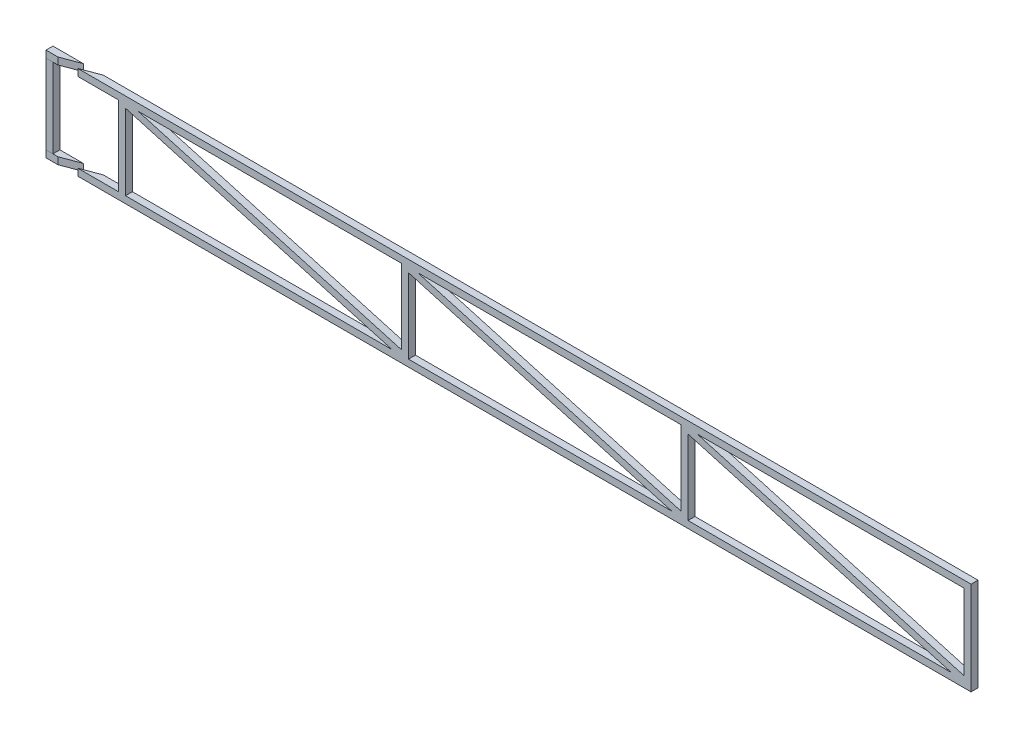
SolidWorks part; units mm, degrees
material "Balsa"
ref_plane "Front Plane" through (0, 0, 0) normal (0, 0, 1) x (1, 0, 0)
ref_plane "Top Plane" through (0, 0, 0) normal (0, 1, 0) x (1, 0, 0)
ref_plane "Right Plane" through (0, 0, 0) normal (1, 0, 0) x (0, 0, -1)
sketch "Sketch1" plane through (0, 0, 0) normal (0, 0, 1) x (1, 0, 0)
  line L0 (-18.175, 48.175) -> (18.175, 48.175)
  line L4 (405, 11.825) -> (405, 15)
  line L5 (-15, 45) -> (15, 45)
  line L7 (-15, 15) -> (15, 15)
  line L10 (405, 11.825) -> (405, 15)
  line L14 (-18.175, 11.825) -> (18.175, 11.825)
  line L16 (18.175, 48.175) -> (405, 48.175)
  line L17 (18.175, 11.825) -> (405, 11.825)
  line L18 (15, 45) -> (405, 45)
  line L19 (15, 15) -> (405, 15)
  line L20 (-18.175, 48.175) -> (-18.175, 45)
  line L21 (-18.175, 48.175) -> (-18.175, 11.825) construction
  line L22 (-15, 45) -> (-15, 15) construction
  line L23 (15, 45) -> (15, 15) construction
  line L24 (-18.175, 45) -> (-15, 45)
  line L25 (18.175, 48.175) -> (18.175, 11.825) construction
  line L26 (405, 45) -> (405, 48.175)
  line L27 (405, 45) -> (405, 48.175)
  line L28 (-18.175, 11.825) -> (-18.175, 15)
  line L29 (-18.175, 15) -> (-15, 15)
  point P4 (0, 30)
  dimension "D3" = 30
  dimension "D5" = 3.175
extrude "Boss-Extrude1" add sketch "Sketch1" along normal blind 3.175 contours L18 L26 L16 L0 L20 L24 L5 | L29 L28 L14 L17 L4 L19 L7
sketch "Sketch2" plane through (0, 0, 3.175) normal (0, 0, 1) x (1, 0, 0)
  line L0 (-18.175, 48.175) -> (405, 48.175) construction
  line L1 (-18.175, 11.825) -> (-15, 11.825)
  line L2 (-18.175, 11.825) -> (-18.175, 48.175)
  line L3 (-18.175, 48.175) -> (-15, 48.175)
  line L4 (-15, 11.825) -> (-15, 48.175)
  line L5 (-18.175, 11.825) -> (405, 11.825) construction
  line L6 (-15, 48.175) -> (15, 48.175)
  line L7 (-15, 48.175) -> (-15, 11.825)
  line L8 (-15, 11.825) -> (15, 11.825)
  line L9 (15, 48.175) -> (15, 11.825)
  line L10 (18.175, 30) -> (401.825, 30) construction
  line L11 (15, 48.175) -> (18.175, 48.175)
  line L12 (15, 48.175) -> (15, 11.825)
  line L13 (15, 11.825) -> (18.175, 11.825)
  line L14 (18.175, 48.175) -> (18.175, 11.825)
  line L15 (405, 48.175) -> (401.825, 48.175)
  line L16 (405, 48.175) -> (405, 11.825)
  line L17 (405, 11.825) -> (401.825, 11.825)
  line L18 (401.825, 48.175) -> (401.825, 11.825)
  line L19 (210, 30) -> (210, 38.7375) construction
  line L20 (18.175, 38.7375) -> (210, 38.7375) construction
  line L21 (114.0875, 38.7375) -> (114.0875, 45)
  line L22 (-18.175, 45) -> (405, 45) construction
  line L23 (210, 38.7375) -> (401.825, 38.7375) construction
  line L24 (305.9125, 38.7375) -> (305.9125, 45) construction
  line L25 (115.675, 11.825) -> (120.0251, 11.825)
  line L26 (115.675, 11.825) -> (112.5, 11.825)
  line L27 (115.675, 11.825) -> (115.675, 48.175)
  line L28 (114.1836, 48.175) -> (112.5, 48.175)
  line L29 (112.5, 11.825) -> (112.5, 48.175)
  line L30 (114.0875, 30) -> (113.3243, 38.7375) construction
  line L31 (115.675, 48.175) -> (112.5, 11.825) construction
  line L32 (211.5875, 11.825) -> (208.4125, 11.825)
  line L33 (211.5875, 11.825) -> (211.5875, 48.175)
  line L34 (211.5875, 48.175) -> (208.4125, 48.175)
  line L35 (208.4125, 11.825) -> (208.4125, 48.175)
  line L36 (211.5875, 11.825) -> (209.2368, 38.7375) construction
  line L37 (211.5875, 48.175) -> (208.4125, 11.825) construction
  line L38 (304.325, 11.825) -> (307.5, 11.825)
  line L39 (304.325, 11.825) -> (304.325, 48.175)
  line L40 (304.325, 48.175) -> (307.5, 48.175)
  line L41 (307.5, 11.825) -> (307.5, 48.175)
  line L42 (304.325, 11.825) -> (307.5, 48.175) construction
  line L43 (304.325, 48.175) -> (307.5, 11.825) construction
  line L44 (120.0251, 11.825) -> (208.4125, 46.4699)
  line L45 (111.3249, 11.825) -> (112.5417, 12.3019)
  line L46 (208.4125, 48.175) -> (204.0624, 48.175)
  line L47 (115.675, 13.5301) -> (204.0624, 48.175)
  point P36 (114.0875, 30)
  point P45 (305.9125, 30)
  line B0 (22.5897, 11.825) -> (112.5, 46.4737)
  line B1 (18.175, 13.5263) -> (108.0853, 48.175)
  line B2 (108.0853, 48.175) -> (112.5, 48.175)
  line B3 (18.175, 11.825) -> (22.5897, 11.825)
  line B4 (211.5875, 11.825) -> (215.9376, 11.825)
  line B5 (215.9376, 11.825) -> (304.325, 46.4699)
  line B6 (304.325, 48.175) -> (299.9749, 48.175)
  line B7 (211.5875, 13.5301) -> (299.9749, 48.175)
  line B8 (311.9147, 11.825) -> (401.825, 46.4737)
  line B9 (307.5, 13.5263) -> (397.4103, 48.175)
  line B10 (397.4103, 48.175) -> (401.825, 48.175)
  line B11 (307.5, 11.825) -> (311.9147, 11.825)
  dimension "D1" = 3.175
  dimension "D2" = 30
  dimension "D3" = 3.175
  dimension "D4" = 3.175
  dimension "D5" = 3.175
  dimension "D6" = 3.175
  dimension "D7" = 3.175
  dimension "D8" = 0
  dimension "D10" = 0
  dimension "D9" = 0
  dimension "D11" = 0
sketch_block_instance "Block1-1"
sketch_block "Block1"
sketch_block_instance "Block2-1"
sketch_block "Block2"
sketch_block_instance "Block1-3"
extrude "Boss-Extrude2" add sketch "Sketch2" along normal blind 3.175
sketch "Sketch3" plane through (405, 0, 0) normal (1, 0, 0) x (0, 0, -1)
  line L1 (-6.35, 11.825) -> (-3.175, 11.825)
  line L2 (-6.35, 11.825) -> (-6.35, 8.65)
  line L3 (-6.35, 8.65) -> (-3.175, 8.65)
  line L4 (-3.175, 11.825) -> (-3.175, 8.65)
  line L5 (-6.35, 48.175) -> (-3.175, 48.175)
  line L6 (-6.35, 48.175) -> (-6.35, 51.35)
  line L7 (-6.35, 51.35) -> (-3.175, 51.35)
  line L8 (-3.175, 48.175) -> (-3.175, 51.35)
  dimension "D1" = 3.175
  dimension "D2" = 3.175
extrude "Boss-Extrude8" add sketch "Sketch3" against normal up to surface (423.175 mm away) separate body contours L8 L7 L6 M2 | L4 L2 L3 M4 up to face at (-18.175, 30, 2.3812)
sketch "Sketch4" plane through (405, 0, 0) normal (1, 0, 0) x (0, 0, -1)
  line L1 (-3.175, 48.175) -> (0, 48.175)
  line L2 (-3.175, 48.175) -> (-3.175, 11.825)
  line L3 (-3.175, 11.825) -> (0, 11.825)
  line L4 (0, 48.175) -> (0, 11.825)
extrude "Cut-Extrude1" cut sketch "Sketch4" against normal through all
sketch "Sketch5" plane through (0, 8.65, 0) normal (0, -1, 0) x (1, 0, 0)
  line L17 (193.4125, 3.175) -> (193.4125, -106.4437) construction
  line L22 (-26.8415, 33.7017) -> (-103.7417, -72.6912)
  line L24 (377.5812, -136.0518) -> (376.4702, -139.0261)
  line L25 (-18.175, 6.35) -> (406.5875, 6.35)
  line L26 (405, 3.175) -> (-18.175, 3.175)
  line L27 (405, 6.35) -> (-18.175, 6.35)
  line L28 (377.5812, -136.0518) -> (4.8614, 3.175)
  line L29 (-12.7117, 6.35) -> (-26.8415, 33.7017)
  line L30 (403.4125, 6.35) -> (403.4125, -137.0625)
  line L31 (376.4702, -139.0261) -> (-4.212, 3.175)
  line L32 (-12.7117, 6.35) -> (-3.6383, 6.35)
  line L33 (406.5875, 6.35) -> (406.5875, -140.2375)
  line L34 (4.8614, 3.175) -> (-3.6383, 6.35)
  line L35 (-4.212, 3.175) -> (-12.7117, 6.35)
  line L36 (405, 6.35) -> (405, -138.65)
  arc A1 (372.1591, -137.4157) -> (373.2701, -134.4414) centre (380, -138.65) cw
extrude "Cut-Extrude7" cut sketch "Sketch5" against normal blind 3.175 contours L35 L26 L34 M6
sketch "Sketch9" plane through (0, 51.35, 0) normal (0, 1, 0) x (1, 0, 0)
  line L0 (391.037, -3.175) -> (399.5367, -6.35) construction
  line L1 (391.037, -3.175) -> (399.5367, -6.35)
  line L2 (381.9636, -3.175) -> (390.4633, -6.35) construction
  line L3 (391.037, -3.175) -> (399.5367, -6.35)
  line L4 (381.9636, -3.175) -> (390.4633, -6.35)
  line L5 (381.9636, -3.175) -> (391.037, -3.175)
  line L6 (399.5367, -6.35) -> (390.4633, -6.35)
  line L7 (-4.212, -3.175) -> (-12.7117, -6.35) construction
  line L8 (4.8614, -3.175) -> (-3.6383, -6.35) construction
  line L9 (-4.212, -3.175) -> (-12.7117, -6.35)
  line L10 (4.8614, -3.175) -> (-3.6383, -6.35)
  line L11 (-12.7117, -6.35) -> (-3.6383, -6.35)
extrude "Cut-Extrude8" cut sketch "Sketch9" against normal blind 3.175 contours L10 L9 M1 M3
ref_plane "Plane4" through (193.4125, 0, 0) normal (-1, 0, 0) x (0, 0, 1)
ref_plane "Plane5" through (405, 11.825, 3.175) normal (0, 1, 0) x (1, 0, 0)
sketch "Sketch11" plane through (0, 0, 3.175) normal (0, 0, -1) x (-1, 0, 0)
  line L1 (-405, 11.825) -> (-18.175, 11.825)
  line L2 (-405, 11.825) -> (-405, 48.175)
  line L3 (-405, 48.175) -> (-18.175, 48.175)
  line L4 (-18.175, 11.825) -> (-18.175, 48.175)
extrude "Boss-Extrude9" add sketch "Sketch11" against normal blind 3.175
sketch "Sketch12" plane through (0, 0, 3.175) normal (0, 0, -1) x (-1, 0, 0)
  line L0 (-146.06, 11.825) -> (-146.06, 48.175)
  line L1 (-15, 11.825) -> (-18.175, 11.825)
  line L2 (-15, 11.825) -> (-15, 48.175)
  line L3 (-15, 48.175) -> (-18.175, 48.175)
  line L4 (-18.175, 11.825) -> (-18.175, 48.175)
  line L5 (-18.175, 48.175) -> (-401.83, 48.175)
  line L6 (-18.175, 48.175) -> (-18.175, 11.825)
  line L7 (-18.175, 11.825) -> (-401.83, 11.825)
  line L8 (-401.83, 48.175) -> (-401.83, 11.825)
  line L9 (-273.945, 11.825) -> (-273.945, 48.175)
  line L10 (-18.175, 48.175) -> (-146.06, 11.825)
  line L11 (-146.06, 48.175) -> (-273.945, 11.825)
  line L12 (-273.945, 48.175) -> (-401.83, 11.825)
  line L13 (-18.609, 49.702) -> (-144.4725, 13.9266)
  line L14 (-144.4725, 13.9266) -> (-144.4725, 50.2766)
  line L15 (-144.4725, 50.2766) -> (-272.3575, 13.9266)
  line L16 (-272.3575, 13.9266) -> (-272.3575, 50.2766)
  line L17 (-272.3575, 50.2766) -> (-402.264, 13.352)
  line L18 (-17.741, 46.648) -> (-147.6475, 9.7234)
  line L19 (-147.6475, 9.7234) -> (-147.6475, 46.0734)
  line L20 (-147.6475, 46.0734) -> (-275.5325, 9.7234)
  line L21 (-275.5325, 9.7234) -> (-275.5325, 46.0734)
  line L22 (-275.5325, 46.0734) -> (-401.396, 10.298)
  point P8 (-146.06, 11.825)
  point P9 (-273.945, 11.825)
  dimension "D1" = 3.175
  dimension "D2" = 383.655
  dimension "D3" = 1.5875
  dimension "D4" = 1.5875
extrude "Cut-Extrude9" cut sketch "Sketch12" against normal blind 3.175 contours L4 L18 L7 | L14 L13 L5 | L19 L20 L7 | L16 L15 L5 | L21 L22 L7 | L17 L5 L8
